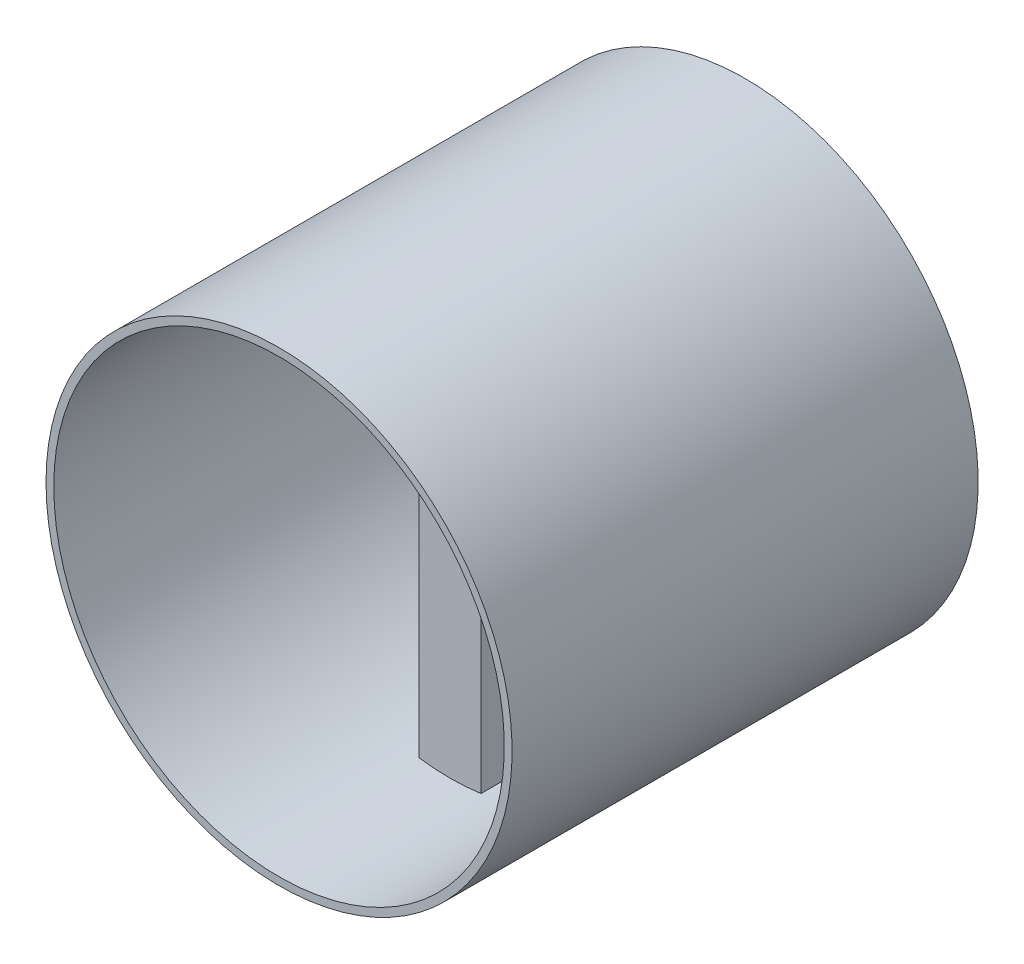
SolidWorks part; units mm, degrees
ref_plane "Plan de face" through (0, 0, 0) normal (0, 0, 1) x (1, 0, 0)
ref_plane "Plan de dessus" through (0, 0, 0) normal (0, 1, 0) x (1, 0, 0)
ref_plane "Plan de droite" through (0, 0, 0) normal (1, 0, 0) x (0, 0, -1)
sketch "Esquisse1" plane through (0, 0, 0) normal (0, 0, 1) x (1, 0, 0)
  line L1 (0, 0) -> (8, 0)
  line L2 (0, 0) -> (0, 59)
  line L3 (0, 59) -> (8, 59)
  line L4 (8, 0) -> (8, 59)
  dimension "D1" = 59
  dimension "D2" = 8
extrude "Boss.-Extru.1" add sketch "Esquisse1" along normal blind 60
sketch "Esquisse3" plane through (0, 0, 0) normal (0, 0, -1) x (-1, 0, 0)
  line L0 (-4, 59) -> (-4, 0) construction
  line L1 (-8, 59) -> (0, 59) construction
  line L2 (0, 0) -> (-8, 0) construction
  line L3 (0, 29.5) -> (-8, 29.5) construction
  line L4 (0, 59) -> (0, 0) construction
  line L5 (-8, 0) -> (-8, 59) construction
  circle A0 centre (-4, 29.5) radius 30
  circle A1 centre (-4, 29.5) radius 29
  dimension "D1" = 60
  dimension "D2" = 58
extrude "Boss.-Extru.2" add sketch "Esquisse3" against normal blind 60
sketch "Esquisse4" plane through (0, 0, 0) normal (0, 0, -1) x (-1, 0, 0)
  line L0 (-4, -0.5) -> (-4, 59.5) construction
  line L1 (-43.5151, 29.5) -> (32.2355, 29.5) construction
  circle A0 centre (-4, 29.5) radius 30 construction
  circle A5 centre (-4, 29.5) radius 29
  dimension "D1" = 58
extrude "Enlèv. mat.-Extru.3" cut sketch "Esquisse4" against normal blind 30
sketch "Esquisse5" plane through (0, 0, 30) normal (0, 0, -1) x (-1, 0, 0)
  line L0 (-4, 58.5) -> (-4, 0.5) construction
  line L1 (25, 29.5) -> (-33, 29.5) construction
  line L3 (-6, 43) -> (-6.9673, 29.942)
  line L5 (-6, 16) -> (-6.9673, 29.058)
  line L6 (-1.0327, 29.942) -> (-2, 43)
  line L7 (-2, 16) -> (-1.0327, 29.058)
  arc A0 (0, 58.2228) -> (-8, 58.2228) centre (-4, 29.5) ccw construction
  arc A1 (-8, 0.7772) -> (0, 0.7772) centre (-4, 29.5) ccw construction
  circle A2 centre (-4, 29.5) radius 29 construction
  arc A3 (-6.9673, 29.942) -> (-6.9673, 29.058) centre (-4, 29.5) ccw
  arc A4 (-2, 43) -> (-6, 43) centre (-4, 43) ccw
  arc A5 (-2, 16) -> (-6, 16) centre (-4, 16) cw
  arc A7 (-1.0327, 29.942) -> (-1.0327, 29.058) centre (-4, 29.5) cw
  dimension "D1" = 6
  dimension "D2" = 4
  dimension "D3" = 13.5
  dimension "D4" = 13.058
  dimension "D5" = 13.058
  dimension "D6" = 171.527
extrude "Enlèv. mat.-Extru.5" cut sketch "Esquisse5" against normal blind 1.5
sketch "Esquisse6" plane through (0, 0, 60) normal (0, 0, 1) x (1, 0, 0)
  line L0 (4, 59.5) -> (4, -0.5) construction
  line L1 (-25, 29.5) -> (33, 29.5) construction
  circle A0 centre (4, 29.5) radius 30 construction
  arc A1 (0, 58.2228) -> (0, 0.7772) centre (4, 29.5) ccw construction
  arc A2 (8, 0.7772) -> (8, 58.2228) centre (4, 29.5) ccw construction
  circle A3 centre (4, 29.5) radius 29
  dimension "D1" = 58
extrude "Enlèv. mat.-Extru.6" cut sketch "Esquisse6" against normal blind 22
sketch "Esquisse7" plane through (0, 0, 31.5) normal (0, 0, -1) x (-1, 0, 0)
  line L0 (-4, 45) -> (-4, 14) construction
  line L1 (-4, 14) -> (-33, 29.5) construction
  line L2 (-33, 29.5) -> (25, 29.5) construction
  arc A0 (-2, 43) -> (-6, 43) centre (-4, 43) ccw construction
  arc A1 (-6, 16) -> (-2, 16) centre (-4, 16) ccw construction
  circle A2 centre (-4, 29.5) radius 29 construction
  circle A3 centre (-4, 29.5) radius 2
  dimension "D1" = 4
extrude "Enlèv. mat.-Extru.7" cut sketch "Esquisse7" against normal blind 6.5
sketch "Esquisse8" plane through (0, 0, 31.5) normal (0, 0, -1) x (-1, 0, 0)
  line L0 (-4, 45) -> (-4, 14) construction
  line L1 (-33, 29.5) -> (25, 29.5) construction
  arc A0 (-2, 43) -> (-6, 43) centre (-4, 43) ccw construction
  arc A1 (-6, 16) -> (-2, 16) centre (-4, 16) ccw construction
  circle A2 centre (-4, 29.5) radius 29 construction
sketch "Esquisse9" plane through (0, 0, 31.5) normal (0, 0, -1) x (-1, 0, 0)
  line L0 (-23.944, 29.5) -> (17.5488, 29.5) construction
  line L1 (-33, 29.5) -> (25, 29.5) construction
  circle A0 centre (-4, 43) radius 0.5
  circle A1 centre (-4, 16) radius 0.5
  dimension "D1" = 1
  dimension "D2" = 2
extrude "Enlèv. mat.-Extru.8" cut sketch "Esquisse9" against normal blind 4
